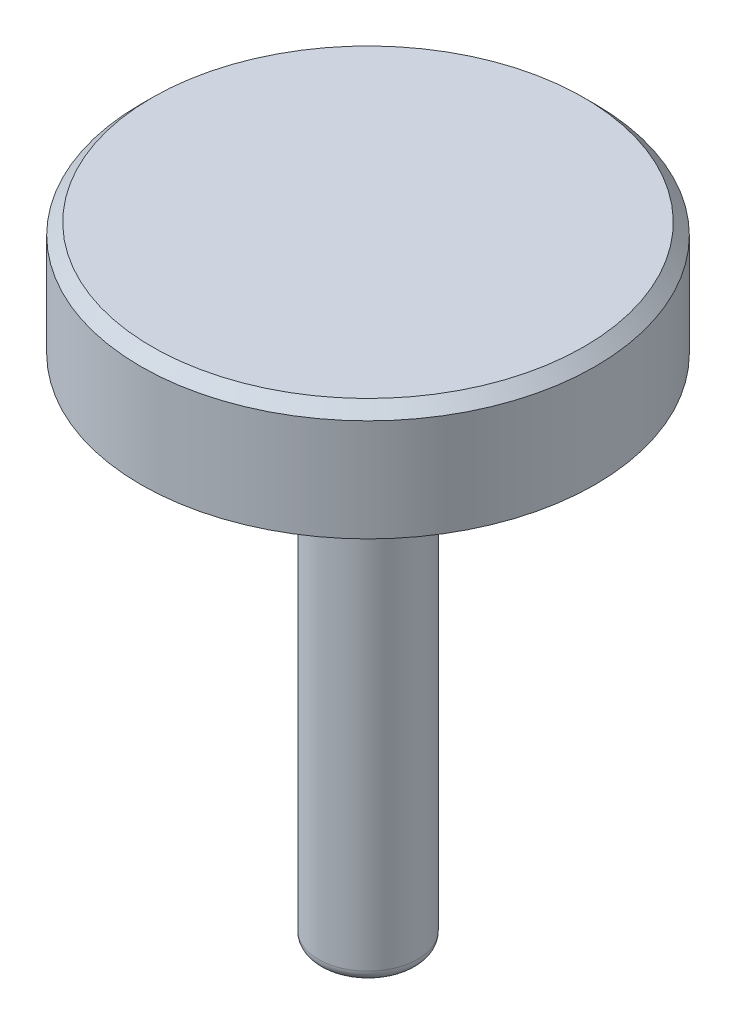
SolidWorks part; units mm, degrees
ref_plane "Front Plane" through (0, 0, 0) normal (0, 0, 1) x (1, 0, 0)
ref_plane "Top Plane" through (0, 0, 0) normal (0, 1, 0) x (1, 0, 0)
ref_plane "Right Plane" through (0, 0, 0) normal (1, 0, 0) x (0, 0, -1)
sketch "Sketch2" plane through (0, 0, 0) normal (0, 0, 1) x (1, 0, 0)
  line L0 (0, 0) -> (0.875, 0)
  line L1 (0.875, 0) -> (0.875, 9)
  line L2 (0.875, 9) -> (4, 9)
  line L3 (4, 9) -> (4, 11)
  line L4 (4, 11) -> (0, 11)
  line L5 (0, 11) -> (0, 0)
  dimension "D1" = 4
  dimension "D2" = 0.875
  dimension "D3" = 2
  dimension "D4" = 9
revolve "Revolve1" add sketch "Sketch2" angle 360 about L5
fillet "Fillet1" radius 0.2 2 edges at (-0.875, 9, 0) (-0.875, 0, 0)
chamfer "Chamfer1" distance 0.2 angle 45 1 edges at (-4, 11, 0)
